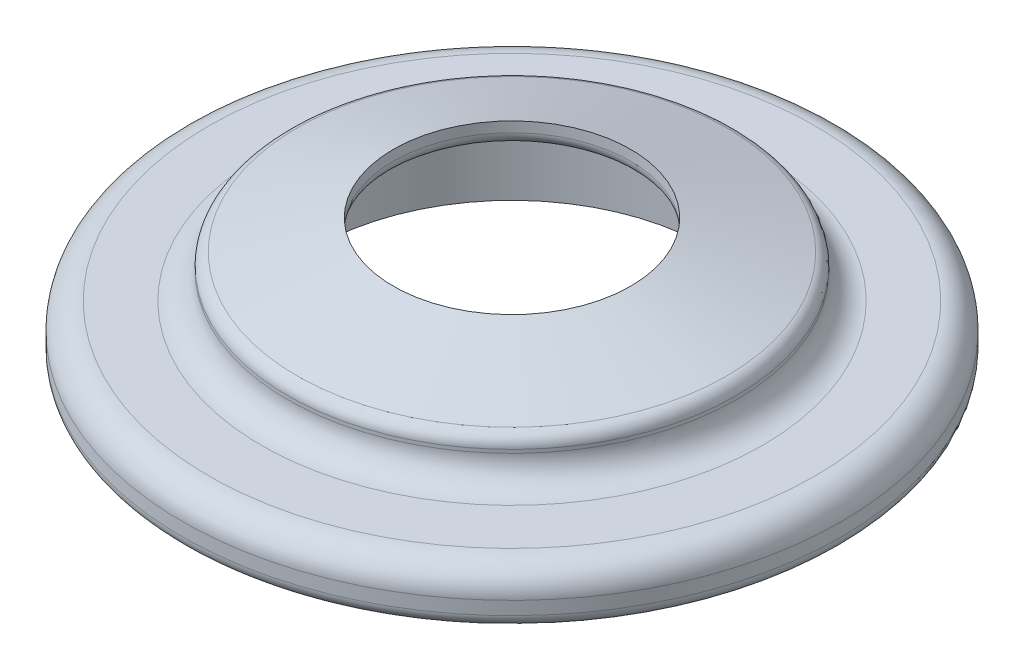
SolidWorks part; units mm, degrees
ref_plane "Front Plane" through (0, 0, 0) normal (0, 0, 1) x (1, 0, 0)
ref_plane "Top Plane" through (0, 0, 0) normal (0, 1, 0) x (1, 0, 0)
ref_plane "Right Plane" through (0, 0, 0) normal (1, 0, 0) x (0, 0, -1)
sketch "Sketch1" plane through (0, 0, 0) normal (0, 0, 1) x (1, 0, 0)
  line L0 (0, 0) -> (0, 22) construction
  line L1 (0, 0) -> (-24, 0)
  line L2 (-25, 1) -> (-25, 2)
  line L3 (-23, 4) -> (-19, 4)
  line L4 (-17, 6) -> (-17, 6.2614)
  line L5 (0, 11) -> (-3.8496, 11)
  line L6 (-4.1437, 10.9558) -> (-16.2941, 7.2172)
  line L7 (0, 0) -> (0, 11)
  arc A0 (-19, 4) -> (-17, 6) centre (-19, 6) ccw
  arc A1 (-25, 2) -> (-23, 4) centre (-23, 2) cw
  arc A2 (-24, 0) -> (-25, 1) centre (-24, 1) cw
  arc A3 (-17, 6.2614) -> (-16.2941, 7.2172) centre (-16, 6.2614) cw
  arc A4 (-3.8496, 11) -> (-4.1437, 10.9558) centre (-3.8496, 10) ccw
  point P8 (0, 0)
  point P9 (-1.9248, 11)
  point P13 (-17, 4)
  point P16 (-25, 4)
  point P19 (-25, 0)
  point P22 (-17, 7)
  point P25 (-4, 11)
  dimension "D7" = 2
  dimension "D8" = 2
  dimension "D9" = 1
  dimension "D10" = 1
  dimension "D11" = 1
  dimension "D1" = 4
  dimension "D2" = 3
  dimension "D3" = 8
  dimension "D4" = 25
  dimension "D5" = 11
  dimension "D6" = 4
revolve "Revolve1" add sketch "Sketch1" angle 360 about L0
sketch "Sketch3" plane through (0, 0, 0) normal (0, 0, 1) x (1, 0, 0)
  line L0 (-24, 0) -> (24, 0) construction
  line L1 (0, 11) -> (0, 0)
  line L2 (-9, 11) -> (-9, 8.6831)
  line L4 (-9.9081, 7.6873) -> (-14.0919, 7.301)
  line L5 (16.2941, 7.2172) -> (-16.2941, 7.2172) construction
  line L6 (-15, 6.3053) -> (-15, 0)
  line L7 (-9, 11) -> (0, 11)
  line L8 (0, 0) -> (-15, 0)
  line L9 (3.8496, 11) -> (-3.8496, 11) construction
  arc A0 (-14.0919, 7.301) -> (-15, 6.3053) centre (-14, 6.3053) ccw
  arc A1 (-9.9081, 7.6873) -> (-9, 8.6831) centre (-10, 8.6831) ccw
  point P4 (0, 0)
  point P5 (0, 0)
  point P10 (0, 0.3548)
  point P12 (0, 0)
  point P13 (-2, 11.1663)
  point P14 (-2, 11)
  point P15 (-15, 7.2172)
  dimension "D3" = 1
  dimension "D4" = 1
  dimension "D6" = 6.3053
  dimension "D1" = 9
  dimension "D2" = 15
revolve "Cut-Revolve2" cut sketch "Sketch3" angle 360 about L1
